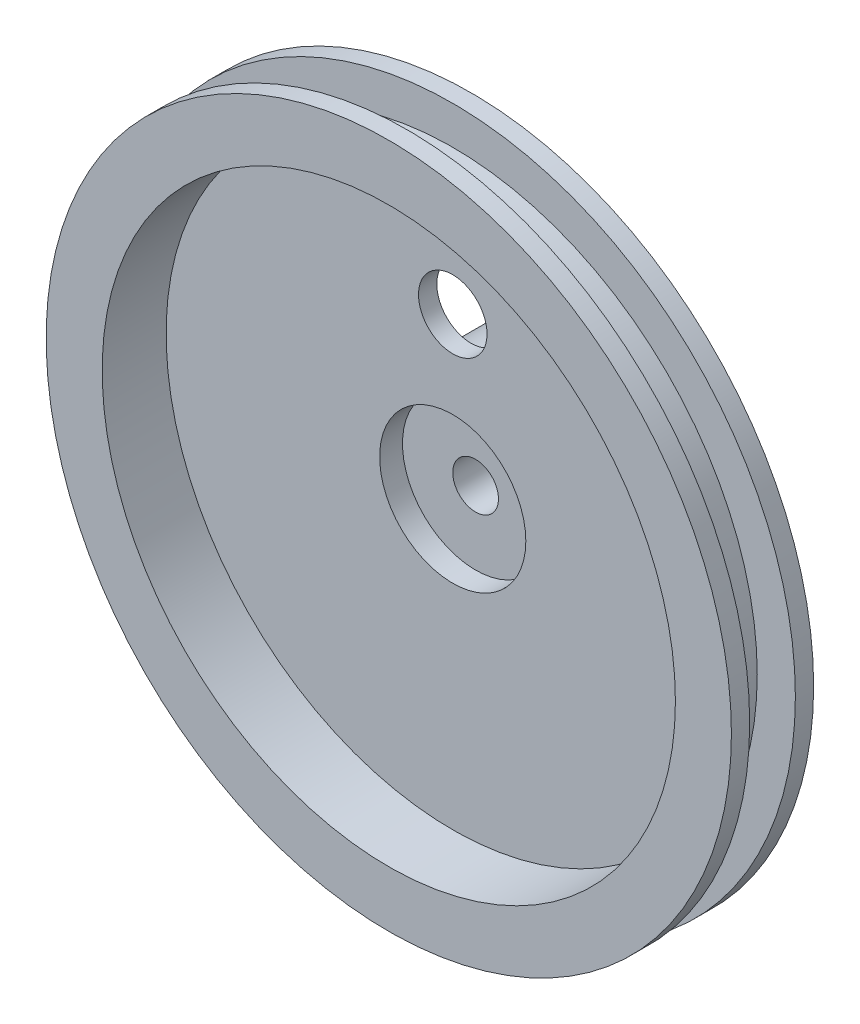
SolidWorks part; units mm, degrees
ref_plane "Front Plane" through (0, 0, 0) normal (0, 0, 1) x (1, 0, 0)
ref_plane "Top Plane" through (0, 0, 0) normal (0, 1, 0) x (1, 0, 0)
ref_plane "Right Plane" through (0, 0, 0) normal (1, 0, 0) x (0, 0, -1)
sketch "Sketch2" plane through (0, 0, 0) normal (1, 0, 0) x (0, 0, -1)
  line L0 (-6.35, 42.3253) -> (0, 42.3253)
  line L1 (-6.35, 42.3253) -> (-6.35, 47.625)
  line L2 (-6.35, 47.625) -> (-8.89, 47.625)
  line L3 (-8.89, 47.625) -> (-8.89, 39.8398)
  line L4 (0, 0) -> (0, 39.8398)
  line L5 (0, 39.8398) -> (-8.89, 39.8398)
  line L6 (0, 42.3253) -> (0, 47.625)
  line L7 (0, 47.625) -> (2.54, 47.625)
  line L8 (2.54, 47.625) -> (2.54, 0)
  line L9 (0, 0) -> (2.54, 0)
  dimension "D1" = 42.3253
  dimension "D2" = 6.35
  dimension "D3" = 47.625
  dimension "D4" = 2.54
revolve "Revolve1" add sketch "Sketch2" angle 360 about L9
sketch "Sketch3" plane through (0, 0, 0) normal (0, 0, 1) x (1, 0, 0)
  circle A0 centre (0, 0) radius 10.16
  dimension "D1" = 20.32
extrude "Cut-Extrude1" cut sketch "Sketch3" against normal blind 2.54
sketch "Sketch4" plane through (0, 0, 0) normal (0, 1, 0) x (1, 0, 0)
  line L0 (0, 0) -> (0, 14.2494) construction
  line L1 (0, 14.2494) -> (-3.175, 14.2494)
  line L2 (-10.16, 3.175) -> (-10.16, 0)
  line L3 (-10.16, 0) -> (-13.335, 0)
  line L4 (0, 14.2494) -> (0, 15.2019)
  line L5 (0, 15.2019) -> (-13.335, 15.2019)
  line L8 (-13.335, 15.2019) -> (-13.335, 0)
  line L9 (-10.16, 3.175) -> (-3.175, 3.175)
  line L10 (-3.175, 3.175) -> (-3.175, 14.2494)
  dimension "D1" = 14.2494
  dimension "D2" = 10.16
  dimension "D4" = 3.175
  dimension "D6" = 15.2019
  dimension "D7" = 3.175
  dimension "D8" = 6.35
revolve "Revolve2" add sketch "Sketch4" angle 360 about L0
sketch "Sketch5" plane through (0, 0, 0) normal (0, 0, 1) x (1, 0, 0)
  circle A0 centre (0, 22.225) radius 4.7625
  dimension "D2" = 9.525
  dimension "D1" = 22.225
extrude "Cut-Extrude2" cut sketch "Sketch5" against normal blind 6.35
sketch "Sketch6" plane through (0, 0, -15.2019) normal (0, 0, -1) x (-1, 0, 0)
  circle A0 centre (0, 0) radius 9.525
  circle A1 centre (0, 0) radius 13.335
  dimension "D1" = 26.67
  dimension "D2" = 19.05
extrude "Boss-Extrude1" add sketch "Sketch6" along normal blind 6.35
sketch "Sketch7" plane through (0, 0, 0) normal (1, 0, 0) x (0, 0, -1)
  circle A0 centre (8.9623, 0) radius 1.27
  dimension "D1" = 2.54
extrude "Cut-Extrude3" cut sketch "Sketch7" against normal blind 25.4
sketch "Sketch8" plane through (0, 0, -21.5519) normal (0, 0, -1) x (-1, 0, 0)
  line L0 (0, 0) -> (0, 15.5858) construction
  line L1 (0, 0) -> (5.9644, 14.3994) construction
  line L2 (0, 0) -> (-5.9644, 14.3994) construction
  line L4 (2.7253, 6.5795) -> (5.9644, 14.3994)
  line L5 (-5.9644, 14.3994) -> (-2.7253, 6.5795)
  circle A0 centre (0, 0) radius 15.5858 construction
  circle A1 centre (0, 0) radius 7.1216 construction
  arc A2 (2.7253, 6.5795) -> (-2.7253, 6.5795) centre (0, 0) ccw
  arc A3 (5.9644, 14.3994) -> (-5.9644, 14.3994) centre (0, 0) ccw
  dimension "D1" = 22.5
  dimension "D2" = 22.5
extrude "Cut-Extrude4" cut sketch "Sketch8" against normal up to surface (6.35 mm away) up to face at (-9.525, 0, -15.2019)
ref_plane "Plane1" through (0, 0, -19.0119) normal (0, 0, -1) x (-1, 0, 0)
sketch "Sketch10" plane through (0, 0, -19.0119) normal (0, 0, -1) x (-1, 0, 0)
  line L0 (0, 0) -> (12.0027, 12.0027) construction
  line L1 (0, 0) -> (16.396, 4.3933) construction
  line L2 (0, 0) -> (0, 19.4152) construction
  line L4 (6.2914, 1.6858) -> (16.396, 4.3933)
  line L5 (4.6056, 4.6056) -> (12.0027, 12.0027)
  line L6 (0, 0) -> (-12.0027, 12.0027) construction
  line L7 (0, 0) -> (-16.396, 4.3933) construction
  line L8 (-4.6056, 4.6056) -> (-12.0027, 12.0027)
  line L10 (-16.396, 4.3933) -> (-6.2914, 1.6858)
  circle A0 centre (0, 0) radius 16.9744 construction
  circle A1 centre (0, 0) radius 6.5133 construction
  arc A2 (6.2914, 1.6858) -> (4.6056, 4.6056) centre (0, 0) ccw
  arc A3 (16.396, 4.3933) -> (12.0027, 12.0027) centre (0, 0) ccw
  arc A4 (-4.6056, 4.6056) -> (-6.2914, 1.6858) centre (0, 0) ccw
  arc A5 (-12.0027, 12.0027) -> (-16.396, 4.3933) centre (0, 0) ccw
  dimension "D1" = 45
  dimension "D2" = 30
  dimension "D3" = 45
  dimension "D4" = 30
extrude "Cut-Extrude5" cut sketch "Sketch10" against normal blind 2.54
sketch "Sketch11" plane through (0, 0, 0) normal (0, 1, 0) x (1, 0, 0)
  circle A0 centre (0, -3.8704) radius 0.889
  dimension "D1" = 1.778
extrude "Cut-Extrude6" cut sketch "Sketch11" along normal blind 55.372
